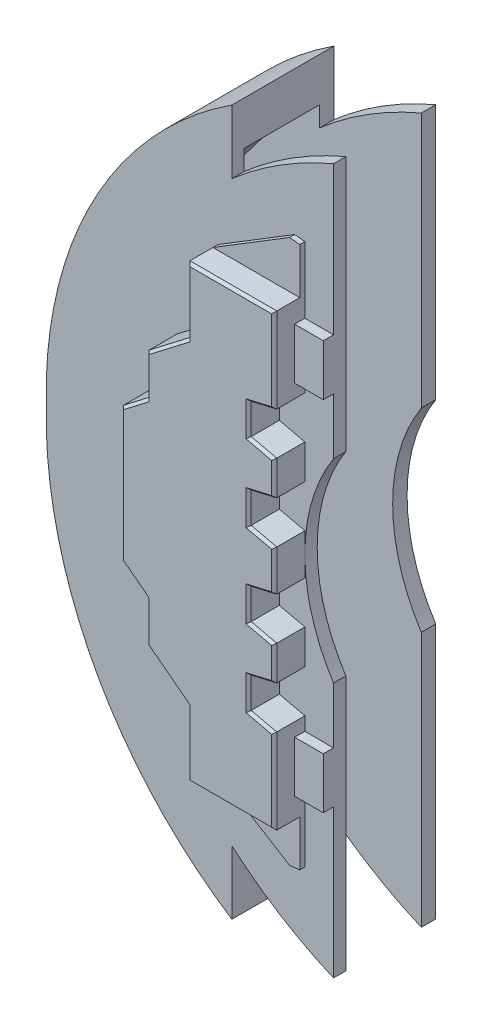
SolidWorks part; units mm, degrees
ref_plane "Front Plane" through (0, 0, 0) normal (0, 0, 1) x (1, 0, 0)
ref_plane "Top Plane" through (0, 0, 0) normal (0, 1, 0) x (1, 0, 0)
ref_plane "Right Plane" through (0, 0, 0) normal (1, 0, 0) x (0, 0, -1)
sketch "Sketch1" plane through (0, 0, 0) normal (0, 0, 1) x (1, 0, 0)
  line L0 (-14.6969, 34.5) -> (-14.6969, 9.5)
  line L1 (-17.5, 0) -> (-42.8029, 0)
  line L2 (-24.6441, 34.5) -> (-24.6441, 28.2651)
  arc A0 (-14.6969, 9.5) -> (-17.5, 0) centre (0, 0) ccw
  circle A1 centre (0, 0) radius 37.5 construction
  arc A2 (-42.8029, 0) -> (-24.6441, 34.5) centre (-2.8149, 0.9816) cw
  arc A3 (-24.6441, 28.2651) -> (-14.6969, 34.5) centre (0, 0) cw
  point P1 (-24.6441, 34.5)
  dimension "D1" = 75
  dimension "D2" = 35
  dimension "D4" = 40
  dimension "D3" = 25
extrude "Boss-Extrude1" add sketch "Sketch1" along normal mid plane 10
sketch "Sketch2" plane through (0, 0, 5) normal (0, 0, 1) x (1, 0, 0)
  line L1 (-17.5, 0) -> (-26, 0)
  line L2 (-17.5, 0) -> (-17.5, 2)
  line L3 (-17.5, 22) -> (-26, 22)
  line L4 (-26, 15.5) -> (-26, 22)
  line L8 (-20, 5.5779) -> (-20, 2.5779)
  line L9 (-20, 2.5779) -> (-17.5, 2)
  line L10 (-26, 15.5) -> (-30.0015, 12.4219)
  line L11 (-30.0015, 12.4219) -> (-30.0015, 8.4219)
  line L12 (-30.0015, 8.4219) -> (-32.5, 6.5)
  line L13 (-32.5, 6.5) -> (-32.5, 0)
  line L14 (-42.8029, 0) -> (-17.5, 0) construction
  line L15 (-17.5, 15) -> (-17.5, 22)
  line L17 (-17.5, 15) -> (-17.5, 13.6803)
  line L18 (-20, 5.5779) -> (-17.5, 6.1557)
  line L19 (-17.5, 6.1557) -> (-17.5, 9.5245)
  line L20 (-17.5, 9.5245) -> (-20, 10.1024)
  line L21 (-20, 10.1024) -> (-20, 13.1024)
  line L22 (-20, 13.1024) -> (-17.5, 13.6803)
  line L23 (-17.5, 13.6803) -> (-17.5, 15)
  line L24 (-17.5, 9.5245) -> (-17.5, 6.1557)
  line M6 (-42.8029, 0) -> (-17.5, 0)
  dimension "D1" = 8.5
  dimension "D2" = 22
  dimension "D3" = 7
  dimension "D4" = 3
  dimension "D5" = 2.5
  dimension "D7" = 2
  dimension "D8" = 6.5
  dimension "D9" = 6.5
  dimension "D10" = 4
  dimension "D11" = 15
  dimension "D12" = 3
extrude "Boss-Extrude2" add sketch "Sketch2" along normal blind 3 contours L21 L22 L17 L15 L3 L4 L10 L11 L12 L13 L2 L9 L8 L18 L19 L20 M6
sketch "Sketch3" plane through (0, 0, 5) normal (0, 0, 1) x (1, 0, 0)
  line L0 (-17.5, 22) -> (-17.5, 13.6803) construction
  line L1 (-17.5, 20) -> (-14.6969, 20)
  line L2 (-17.5, 20) -> (-17.5, 15)
  line L3 (-17.5, 15) -> (-14.6969, 15)
  line L4 (-14.6969, 20) -> (-14.6969, 15)
  line L5 (-14.6969, 9.5) -> (-14.6969, 34.5) construction
  dimension "D1" = 15
  dimension "D2" = 5
extrude "Boss-Extrude3" add sketch "Sketch3" along normal blind 1
sketch "Sketch4" plane through (0, 0, 5) normal (0, 0, 1) x (1, 0, 0)
  line L0 (-26, 22) -> (-18.4951, 26.5993)
  line L1 (-18.4951, 26.5993) -> (-17.5, 26.5)
  line L2 (-17.5, 26.5) -> (-17.5, 22)
  line L3 (-26, 22) -> (-17.5, 22)
  dimension "D1" = 1
  dimension "D2" = 4.5
extrude "Boss-Extrude4" add sketch "Sketch4" along normal blind 0.5
sketch "Sketch5" plane through (0, 0, 0) normal (1, 0, 0) x (0, 0, -1)
  line L0 (-3.7959, 0) -> (3.5902, 0)
  line L2 (-3.7959, 0) -> (-3.7959, 39)
  line L3 (-3.7959, 39) -> (3.5902, 39)
  line L4 (3.5902, 0) -> (3.5902, 39)
  line L5 (0, 0) -> (3.5902, 39) construction
  line L6 (-3.7959, 39) -> (0, 0) construction
  line L7 (-5, 0) -> (5, 0) construction
  line L8 (0, 0) -> (0, 13.109) construction
  point P0 (0, 0)
  dimension "D1" = 39
revolve "Cut-Revolve1" cut sketch "Sketch5" angle 360 about L0
mirror "Mirror1" about plane through (0, 0, 0) normal (0, 1, 0) of "Cut-Revolve1", "Boss-Extrude4", "Boss-Extrude3", "Boss-Extrude2", "Boss-Extrude1"
chamfer "Chamfer2" distance 0.25 angle 45 28 edges at (-18.75, 9.8135, 8) (-17.5, 7.8401, 8) (-18.75, 5.8668, 8) (-20, 4.0779, 8) (-18.75, 2.2889, 8) (-17.5, 0, 8) (-18.75, -2.2889, 8) (-20, -4.0779, 8) (-18.75, -5.8668, 8) (-17.5, -7.8401, 8) (-18.75, -9.8135, 8) (-20, -11.6024, 8) (-18.75, -13.3914, 8) (-17.5, -17.8401, 8) (-21.75, -22, 8) (-26, -18.75, 8) (-28.0008, -13.961, 8) (-30.0015, -10.4219, 8) (-31.2508, -7.461, 8) (-32.5, 0, 8) (-31.2508, 7.461, 8) (-30.0015, 10.4219, 8) (-28.0008, 13.961, 8) (-26, 18.75, 8) (-21.75, 22, 8) (-17.5, 17.8401, 8) (-18.75, 13.3914, 8) (-20, 11.6024, 8)
